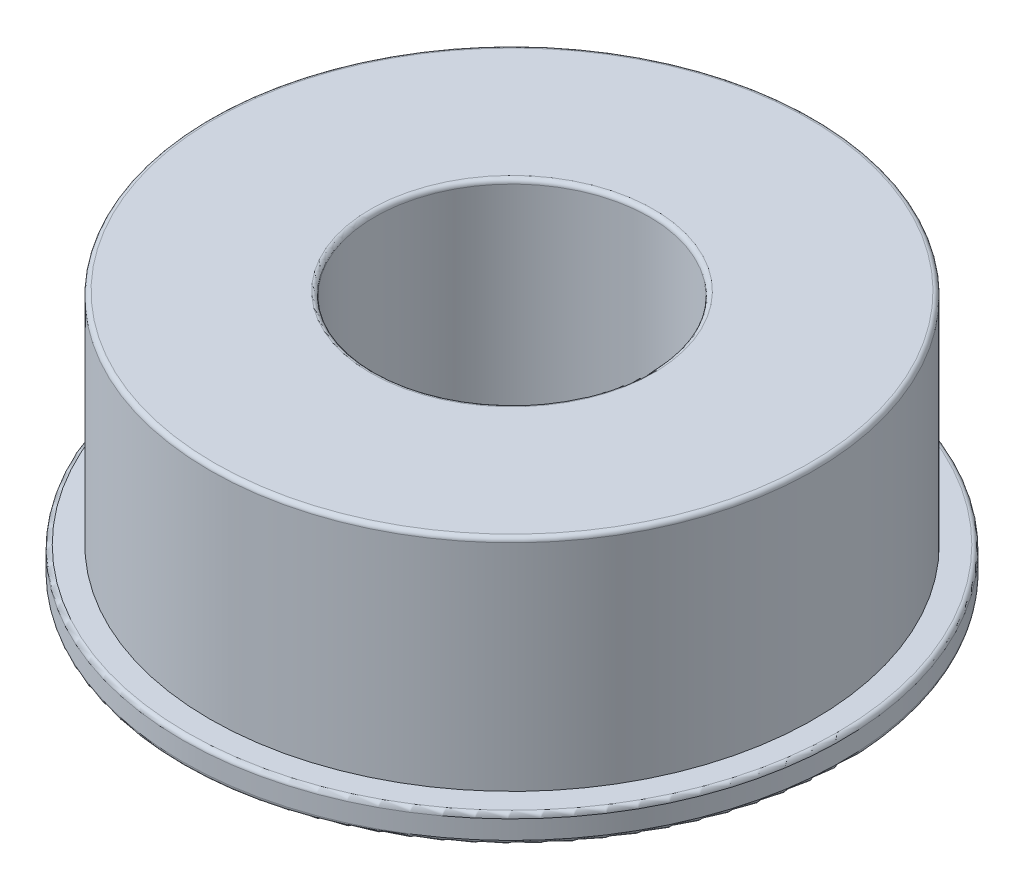
SolidWorks part; units mm, degrees
ref_plane "Front Plane" through (0, 0, 0) normal (0, 0, 1) x (1, 0, 0)
ref_plane "Top Plane" through (0, 0, 0) normal (0, 1, 0) x (1, 0, 0)
ref_plane "Right Plane" through (0, 0, 0) normal (1, 0, 0) x (0, 0, -1)
sketch "Sketch1" plane through (0, 0, 0) normal (0, 1, 0) x (1, 0, 0)
  circle A0 centre (0, 0) radius 19.05
  dimension "D1" = 38.1
extrude "Boss-Extrude1" add sketch "Sketch1" along normal blind 1.5875
sketch "Sketch2" plane through (0, 1.5875, 0) normal (0, 1, 0) x (1, 0, 0)
  circle A0 centre (0, 0) radius 17.4625
  dimension "D1" = 34.925
extrude "Boss-Extrude2" add sketch "Sketch2" along normal blind 12.7
sketch "Sketch3" plane through (0, 14.2875, 0) normal (0, 1, 0) x (1, 0, 0)
  circle A0 centre (0, 0) radius 7.9375
  dimension "D1" = 15.875
extrude "Cut-Extrude1" cut sketch "Sketch3" against normal through all
fillet "Fillet1" radius 0.254 4 edges at (0, 14.2875, 7.9375) (0, 0, 19.05) (0, 1.5875, 19.05) (0, 14.2875, 17.4625)
